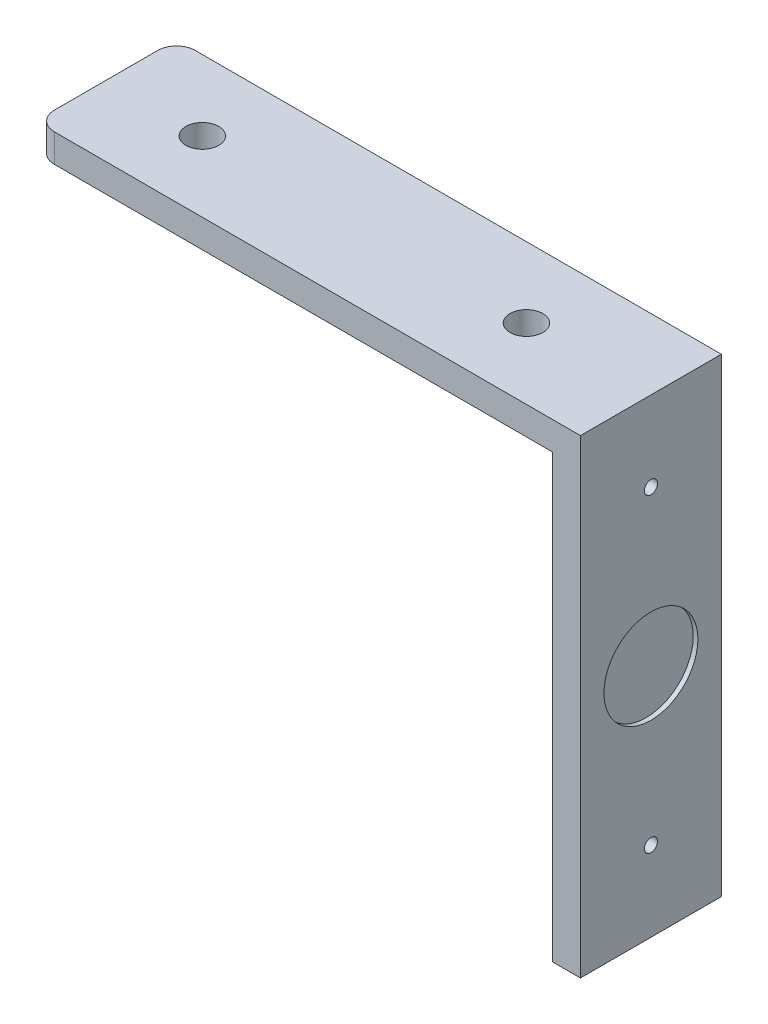
SolidWorks part; units mm, degrees
ref_plane "Front Plane" through (0, 0, 0) normal (0, 0, 1) x (1, 0, 0)
ref_plane "Top Plane" through (0, 0, 0) normal (0, 1, 0) x (1, 0, 0)
ref_plane "Right Plane" through (0, 0, 0) normal (1, 0, 0) x (0, 0, -1)
sketch "Sketch1" plane through (0, 0, 0) normal (0, 1, 0) x (1, 0, 0)
  line L1 (-13.7258, -5.6728) -> (41.2742, -5.6728)
  line L2 (-13.7258, -5.6728) -> (-13.7258, -20.6728)
  line L3 (-13.7258, -20.6728) -> (41.2742, -20.6728)
  line L4 (41.2742, -5.6728) -> (41.2742, -20.6728)
  dimension "D1" = 55
  dimension "D2" = 15
extrude "Boss-Extrude1" add sketch "Sketch1" along normal blind 3
fillet "Fillet8" radius 2 1 edges at (-13.7258, 1.5, 5.6728)
fillet "Fillet9" radius 2 1 edges at (-13.7258, 1.5, 20.6728)
sketch "Sketch2" plane through (0, 3, 0) normal (0, 1, 0) x (1, 0, 0)
  line L0 (14.7742, -5.6728) -> (14.7742, -13.1728) construction
  line L1 (41.2742, -5.6728) -> (-11.7258, -5.6728) construction
  line L2 (14.7742, -13.1728) -> (-3.4758, -13.1728) construction
  circle A0 centre (-3.4758, -13.1728) radius 1.75
  dimension "D1" = 18.25
extrude "Cut-Extrude1" cut sketch "Sketch2" against normal blind 3
ref_plane "Plane1" through (13.7742, 0, 0) normal (-1, 0, 0) x (0, 0, 1)
mirror "Mirror1" about plane through (13.7742, 0, 0) normal (-1, 0, 0) of "Cut-Extrude1"
sketch "Sketch4" plane through (0, 3, 0) normal (0, 1, 0) x (1, 0, 0)
  line L1 (41.2742, -5.6728) -> (44.2742, -5.6728)
  line L2 (41.2742, -5.6728) -> (41.2742, -20.6728)
  line L3 (41.2742, -20.6728) -> (44.2742, -20.6728)
  line L4 (44.2742, -5.6728) -> (44.2742, -20.6728)
  dimension "D1" = 15
  dimension "D2" = 3
extrude "Boss-Extrude2" add sketch "Sketch4" against normal blind 50
ref_plane "Plane3" through (0, -22, 0) normal (0, -1, 0) x (-1, 0, 0)
sketch "Sketch6" plane through (44.2742, 0, 0) normal (1, 0, 0) x (0, 0, -1)
  line L0 (-5.6728, -22) -> (-13.1728, -22) construction
  line L1 (-5.6728, -47) -> (-5.6728, 3) construction
  line L2 (-13.1728, -22) -> (-13.1728, -5.5) construction
  circle A0 centre (-13.1728, -5.5) radius 0.7
  dimension "D1" = 7.5
  dimension "D2" = 16.5
extrude "Cut-Extrude2" cut sketch "Sketch6" against normal blind 50
mirror "Mirror2" about plane through (0, -22, 0) normal (0, -1, 0) of "Cut-Extrude2"
sketch "Sketch7" plane through (44.2742, 0, 0) normal (1, 0, 0) x (0, 0, -1)
  line L0 (-5.6728, 3) -> (-5.6728, -22) construction
  line L1 (-5.6728, -47) -> (-5.6728, 3) construction
  line L2 (-5.6728, -22) -> (-13.1728, -22) construction
  circle A0 centre (-13.1728, -22) radius 5
  dimension "D1" = 7.5
extrude "Cut-Extrude3" cut sketch "Sketch7" against normal blind 0.5
